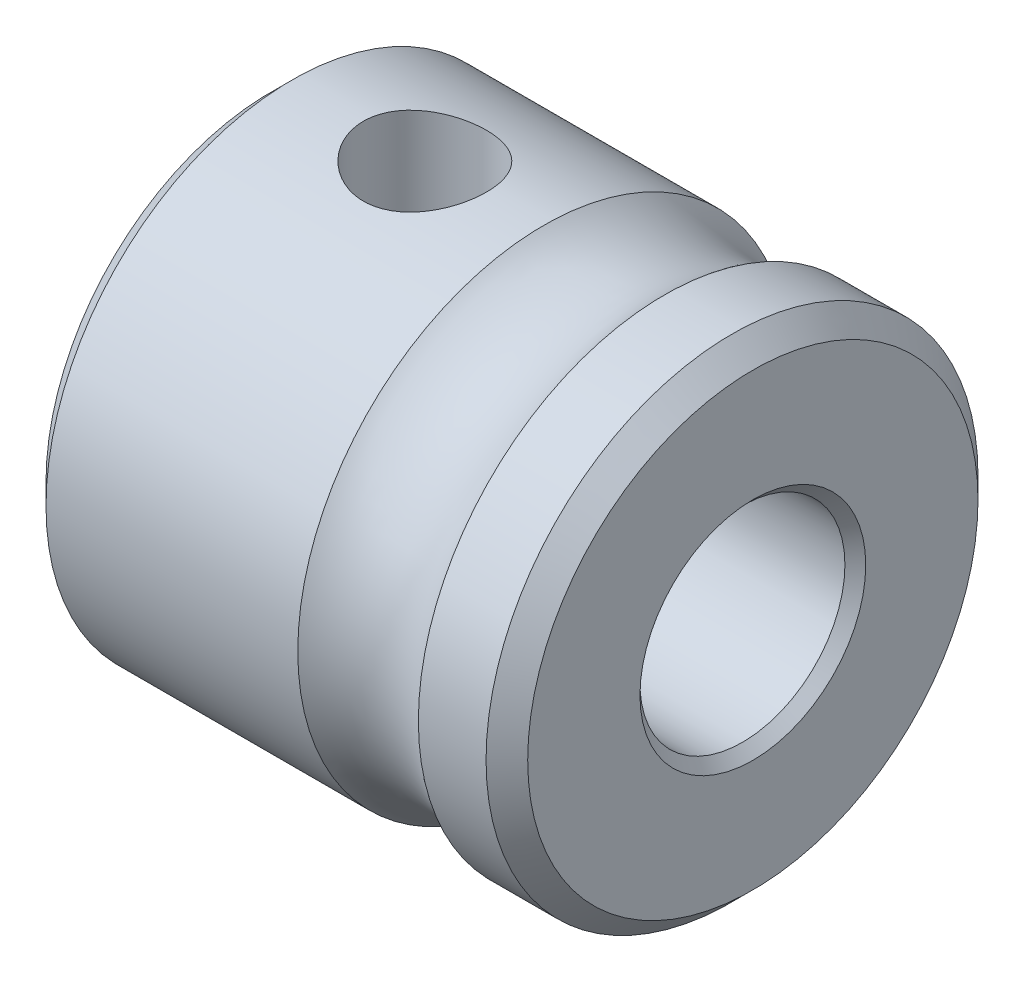
SolidWorks part; units mm, degrees
ref_plane "Front Plane" through (0, 0, 0) normal (0, 0, 1) x (1, 0, 0)
ref_plane "Top Plane" through (0, 0, 0) normal (0, 1, 0) x (1, 0, 0)
ref_plane "Right Plane" through (0, 0, 0) normal (1, 0, 0) x (0, 0, -1)
sketch "Sketch1" plane through (0, 0, 0) normal (1, 0, 0) x (0, 0, -1)
  circle A0 centre (0, 0) radius 6
  circle A1 centre (0, 0) radius 2.5
  dimension "D1" = 5
  dimension "D2" = 12
extrude "Boss-Extrude1" add sketch "Sketch1" against normal blind 11.75
sketch "Sketch2" plane through (0, 0, 0) normal (0, 1, 0) x (1, 0, 0)
  line L0 (-3.6297, 5.5) -> (2.9961, 5.5) construction
  line L1 (0, 0) -> (7.7579, 0) construction
  line L3 (-2.159, 6) -> (0, 6) construction
  line L4 (0, 6) -> (-11.75, 6) construction
  circle A0 centre (-3.6297, 7.913) radius 2.413
  dimension "D2" = 4.826
  dimension "D1" = 5.5
  dimension "D3" = 2.159
revolve "Cut-Revolve1" cut sketch "Sketch2" angle 360 about L1
sketch "Sketch3" plane through (0, 0, 0) normal (0, 1, 0) x (1, 0, 0)
  circle A0 centre (-8, 0) radius 1.5
  dimension "D1" = 3
  dimension "D2" = 8
extrude "Cut-Extrude1" cut sketch "Sketch3" along normal blind 12
chamfer "Chamfer1" distance 0.508 angle 45 2 edges at (-11.75, 0, -6) (0, 0, -6)
chamfer "Chamfer2" distance 0.254 angle 45 1 edges at (0, 0, -2.5)
